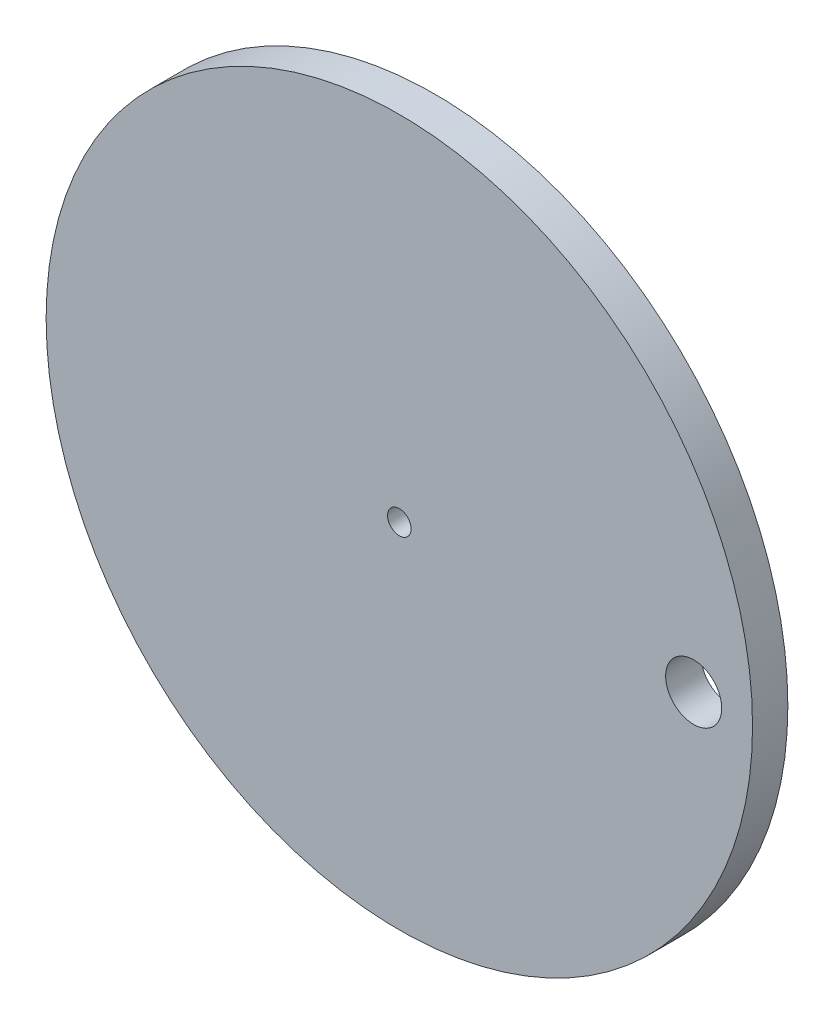
SolidWorks part; units mm, degrees
material "Balsa"
ref_plane "Alzado" through (0, 0, 0) normal (0, 0, 1) x (1, 0, 0)
ref_plane "Planta" through (0, 0, 0) normal (0, 1, 0) x (1, 0, 0)
ref_plane "Vista lateral" through (0, 0, 0) normal (1, 0, 0) x (0, 0, -1)
sketch "Croquis1" plane through (0, 0, 0) normal (0, 0, 1) x (1, 0, 0)
  line L0 (-38.4821, 0) -> (39.007, 0) construction
  line L1 (0, 33.4581) -> (0, -37.9426) construction
  circle A0 centre (0, 0) radius 30
  circle A1 centre (0, 0) radius 1
  circle A2 centre (25, 0) radius 2.3813
  circle A3 centre (0, 0) radius 25 construction
  dimension "D1" = 60
  dimension "D2" = 2
  dimension "D3" = 50
  dimension "D4" = 4.7625
extrude "Saliente-Extruir1" add sketch "Croquis1" along normal blind 3
